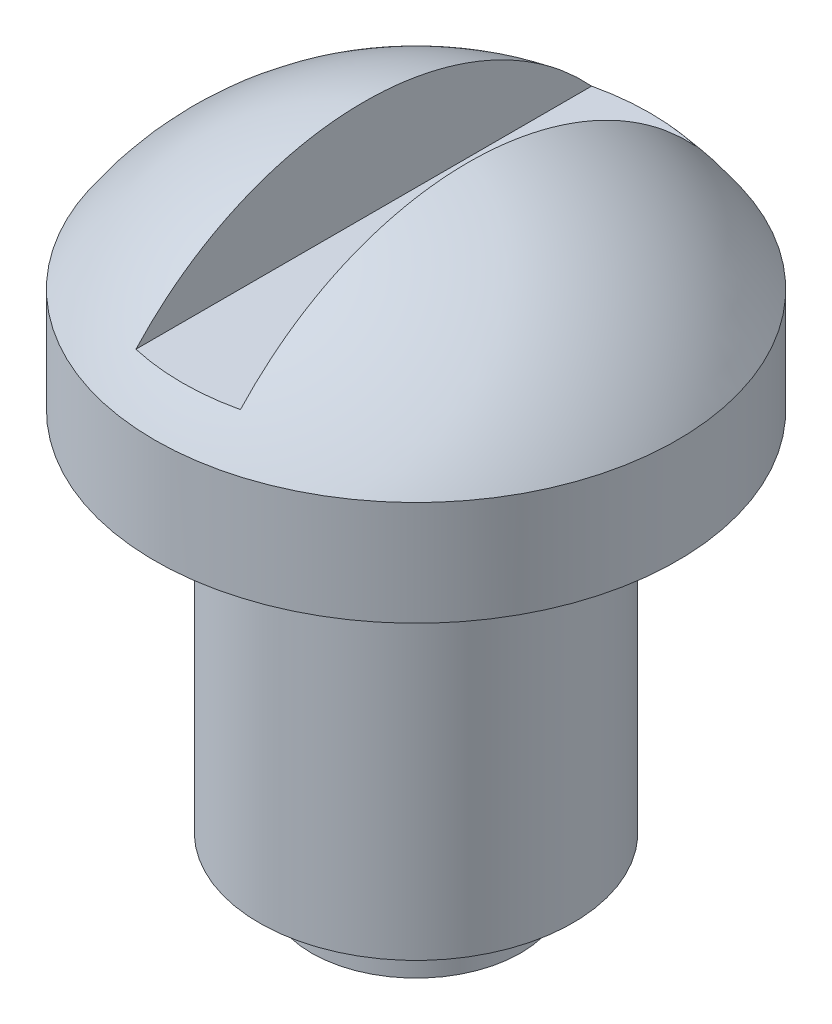
SolidWorks part; units mm, degrees
ref_plane "Front Plane" through (0, 0, 0) normal (0, 0, 1) x (1, 0, 0)
ref_plane "Top Plane" through (0, 0, 0) normal (0, 1, 0) x (1, 0, 0)
ref_plane "Right Plane" through (0, 0, 0) normal (1, 0, 0) x (0, 0, -1)
sketch "Sketch1" plane through (0, 0, 0) normal (0, 0, 1) x (1, 0, 0)
  line L0 (0, 0) -> (2, 0)
  line L1 (2, 0) -> (2, 1)
  line L2 (2, 1) -> (3, 1)
  line L3 (3, 1) -> (3, 8)
  line L4 (3, 8) -> (5, 8)
  line L5 (5, 8) -> (5, 10)
  line L7 (0, 10) -> (0, 0)
  line L8 (0, 10) -> (0, 12.6834)
  arc A0 (5, 10) -> (0, 12.6834) centre (0, 6.6834) ccw
  dimension "D7" = 12
  dimension "D1" = 2
  dimension "D2" = 3
  dimension "D3" = 5
  dimension "D4" = 1
  dimension "D5" = 7
  dimension "D6" = 2
revolve "Revolve1" add sketch "Sketch1" angle 360 about L7
sketch "Sketch3" plane through (0, 8, 0) normal (0, -1, 0) x (1, 0, 0)
  line L1 (1, 7) -> (-1, 7)
  line L2 (1, 7) -> (1, -7)
  line L3 (1, -7) -> (-1, -7)
  line L4 (-1, 7) -> (-1, -7)
  line L5 (1, 7) -> (-1, -7) construction
  line L6 (1, -7) -> (-1, 7) construction
  point P0 (0, 0)
  dimension "D1" = 2
  dimension "D2" = 14
ref_plane "Plane1" through (0, 12.6834, 0) normal (0, 1, 0) x (1, 0, 0)
sketch "Sketch5" plane through (0, 12.6834, 0) normal (0, 1, 0) x (1, 0, 0)
  line L1 (-1, 7) -> (1, 7)
  line L2 (-1, 7) -> (-1, -7)
  line L3 (-1, -7) -> (1, -7)
  line L4 (1, 7) -> (1, -7)
  line L5 (-1, 7) -> (1, -7) construction
  line L6 (-1, -7) -> (1, 7) construction
  point P0 (0, 0)
  dimension "D1" = 2
  dimension "D2" = 14
extrude "Cut-Extrude1" cut sketch "Sketch5" against normal blind 2
